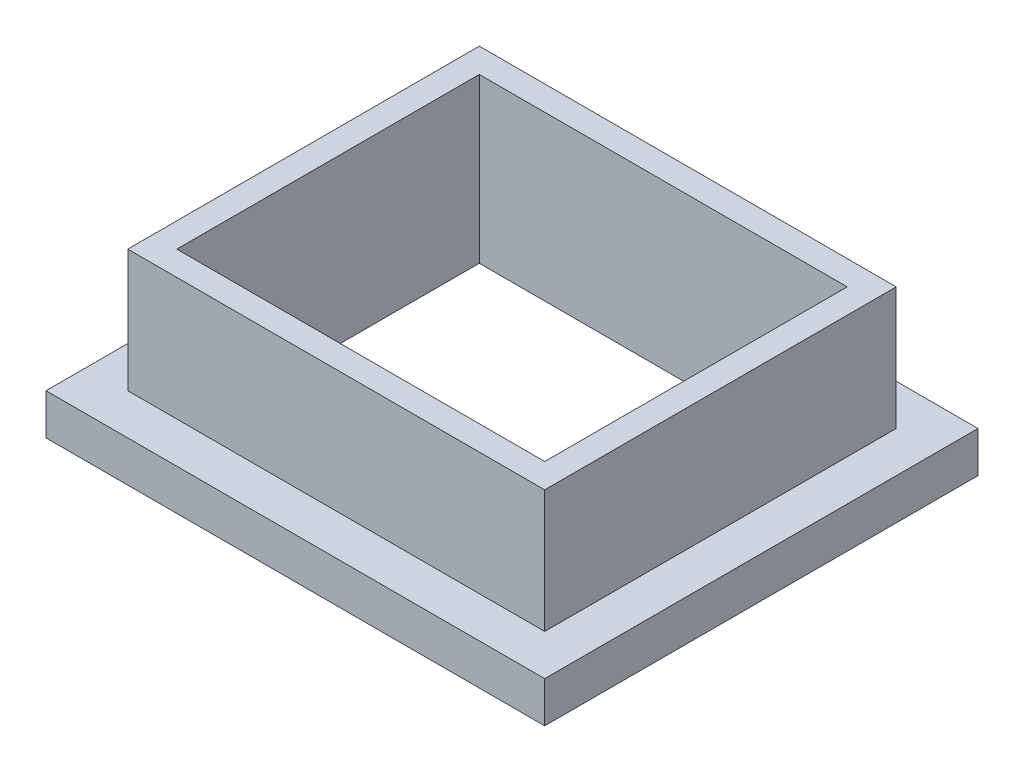
SolidWorks part; units mm, degrees
ref_plane "Front Plane" through (0, 0, 0) normal (0, 0, 1) x (1, 0, 0)
ref_plane "Top Plane" through (0, 0, 0) normal (0, 1, 0) x (1, 0, 0)
ref_plane "Right Plane" through (0, 0, 0) normal (1, 0, 0) x (0, 0, -1)
sketch "Sketch2" plane through (0, 0, 0) normal (0, 1, 0) x (1, 0, 0)
  line L1 (0, 0) -> (61, 0)
  line L2 (0, 0) -> (0, 53)
  line L3 (0, 53) -> (61, 53)
  line L4 (61, 0) -> (61, 53)
  line L5 (5, 48) -> (56, 48)
  line L6 (5, 48) -> (5, 5)
  line L7 (5, 5) -> (56, 5)
  line L8 (56, 48) -> (56, 5)
  dimension "D1" = 61
  dimension "D2" = 53
  dimension "D3" = 5
  dimension "D4" = 5
  dimension "D5" = 51
  dimension "D6" = 43
extrude "Boss-Extrude1" add sketch "Sketch2" along normal blind 5
sketch "Sketch6" plane through (0, 0, 0) normal (0, 1, 0) x (1, 0, 0)
  line L1 (5, 48) -> (56, 48)
  line L2 (5, 48) -> (5, 5)
  line L3 (5, 5) -> (56, 5)
  line L4 (56, 48) -> (56, 5)
  line L5 (8, 45) -> (53, 45)
  line L6 (8, 45) -> (8, 8)
  line L7 (8, 8) -> (53, 8)
  line L8 (53, 45) -> (53, 8)
  dimension "D1" = 3
  dimension "D2" = 3
  dimension "D3" = 3
  dimension "D4" = 3
extrude "Boss-Extrude3" add sketch "Sketch6" along normal blind 20
